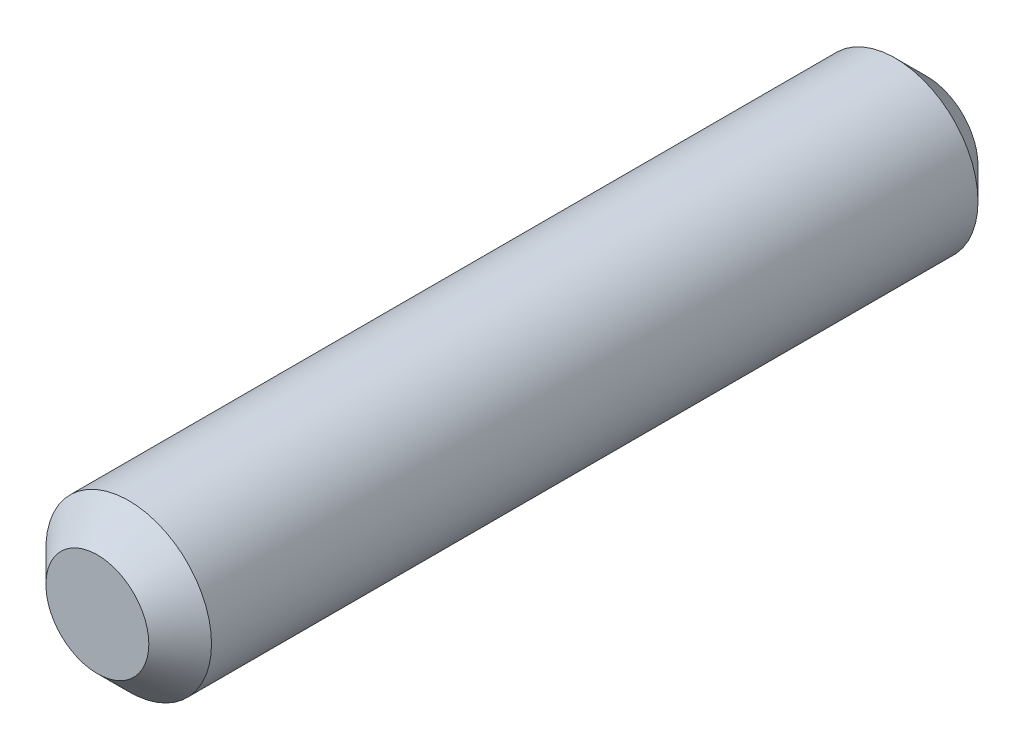
SolidWorks part; units mm, degrees
ref_plane "Front Plane" through (0, 0, 0) normal (0, 0, 1) x (1, 0, 0)
ref_plane "Top Plane" through (0, 0, 0) normal (0, 1, 0) x (1, 0, 0)
ref_plane "Right Plane" through (0, 0, 0) normal (1, 0, 0) x (0, 0, -1)
sketch "Sketch1" plane through (0, 0, 0) normal (0, 0, 1) x (1, 0, 0)
  circle A0 centre (0, 0) radius 1.585
  dimension "D1" = 3.17
extrude "Boss-Extrude1" add sketch "Sketch1" along normal mid plane 15.87
chamfer "Chamfer1" distance 0.6 angle 45 2 edges at (1.585, 0, -7.935) (1.585, 0, 7.935)
